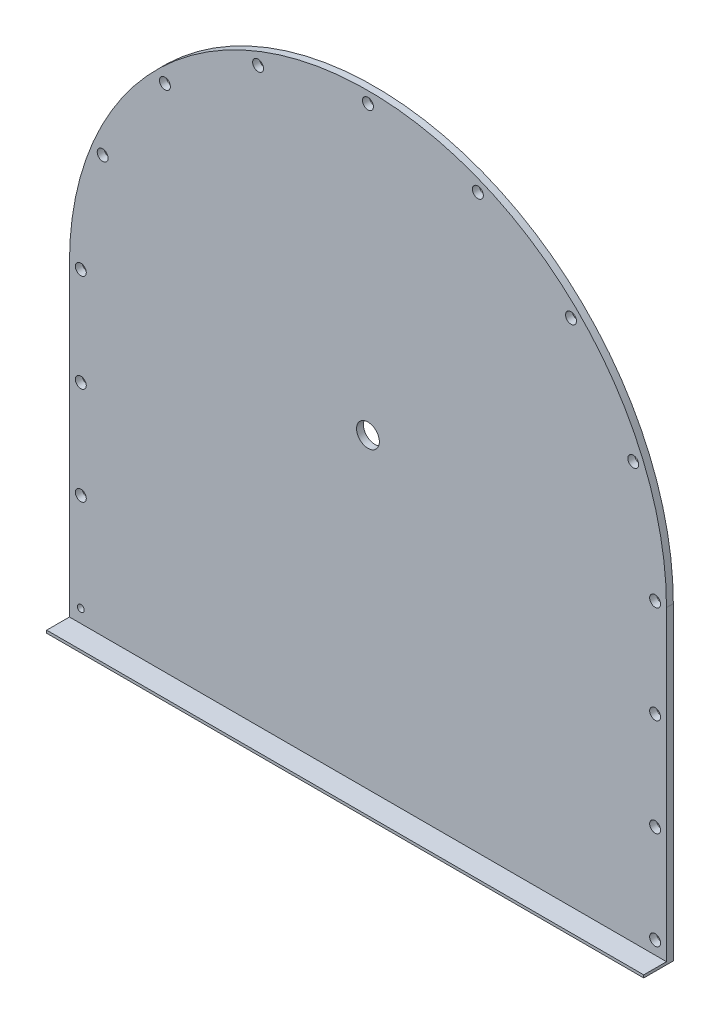
SolidWorks part; units mm, degrees
ref_plane "정면" through (0, 0, 0) normal (0, 0, 1) x (1, 0, 0)
ref_plane "평면" through (0, 0, 0) normal (0, 1, 0) x (1, 0, 0)
ref_plane "우측면" through (0, 0, 0) normal (1, 0, 0) x (0, 0, -1)
sketch "스케치1" plane through (0, 0, 0) normal (1, 0, 0) x (0, 0, -1)
  line L0 (0, 0) -> (65, 0)
  line L1 (65, 0) -> (65, 1336)
  line L2 (0, 6) -> (50, 6)
  line L3 (50, 6) -> (50, 1336)
  line L4 (0, 6) -> (0, 0)
  line L5 (50, 0) -> (50, 680) construction
  line L6 (0, 6) -> (65, 6) construction
  line L8 (65, 1336) -> (50, 1336)
  line L9 (65, 0) -> (65, 680) construction
  dimension "D1" = 6
  dimension "D2" = 65
  dimension "D3" = 15
  dimension "D4" = 1336
extrude "보스-돌출1" add sketch "스케치1" along normal blind 1312
sketch "스케치2" plane through (0, 0, -50) normal (0, 0, 1) x (1, 0, 0)
  circle A0 centre (656, 680) radius 25
  dimension "D1" = 50
  dimension "D2" = 680
  dimension "D3" = 656
extrude "컷-돌출1" cut sketch "스케치2" against normal up to next
sketch "스케치3" plane through (0, 0, -50) normal (0, 0, 1) x (1, 0, 0)
  line L4 (1312, 1336) -> (1312, 680)
  line L5 (1312, 1336) -> (0, 1336)
  line L6 (0, 1336) -> (0, 680)
  arc A0 (1312, 680) -> (0, 680) centre (656, 680) ccw
  line M5 (0, 1336) -> (0, 6)
  line M7 (1312, 6) -> (1312, 1336)
  line M8 (1312, 1336) -> (0, 1336)
  dimension "D1" = 656
  dimension "D3" = 656
  dimension "D2" = 1312
  dimension "D4" = 1336
extrude "컷-돌출2" cut sketch "스케치3" against normal up to next contours A0 L5 M5 | A0 M7 M8
sketch "스케치4" plane through (0, 0, -50) normal (0, 0, 1) x (1, 0, 0)
  line L0 (25, 680) -> (25, 6) construction
  line L1 (1287, 680) -> (1287, 6) construction
  line L5 (25, 35) -> (1287, 35) construction
  line L6 (25, 250) -> (1287, 250) construction
  line L7 (25, 465) -> (1287, 465) construction
  arc A0 (1287, 680) -> (25, 680) centre (656, 680) ccw construction
  circle A1 centre (25, 35) radius 7.5
  circle A2 centre (25, 250) radius 12
  circle A3 centre (25, 465) radius 12
  circle A4 centre (1287, 35) radius 12
  circle A5 centre (1287, 250) radius 12
  circle A6 centre (1287, 465) radius 12
  circle A7 centre (1287, 680) radius 12
  circle A8 centre (25, 680) radius 12
  circle A9 centre (73.032, 921.4732) radius 12
  circle A10 centre (209.8156, 1126.1844) radius 12
  circle A11 centre (414.5268, 1262.968) radius 12
  circle A12 centre (656, 1311) radius 12
  circle A13 centre (897.4732, 1262.968) radius 12
  circle A14 centre (1102.1844, 1126.1844) radius 12
  circle A15 centre (1238.968, 921.4732) radius 12
  circle A16 centre (1287, 680) radius 12
  point P40 (656, 680)
  dimension "D1" = 631
  dimension "D5" = 24
  dimension "D2" = 35
  dimension "D3" = 215
  dimension "D4" = 215
  dimension "D6" = 9
extrude "컷-돌출3" cut sketch "스케치4" against normal up to next contours A1 | A2 | A3 | A8 | A9 | A10 | A11 | A12 | A13 | A14 | A15 | A7 | A6 | A5 | A4
